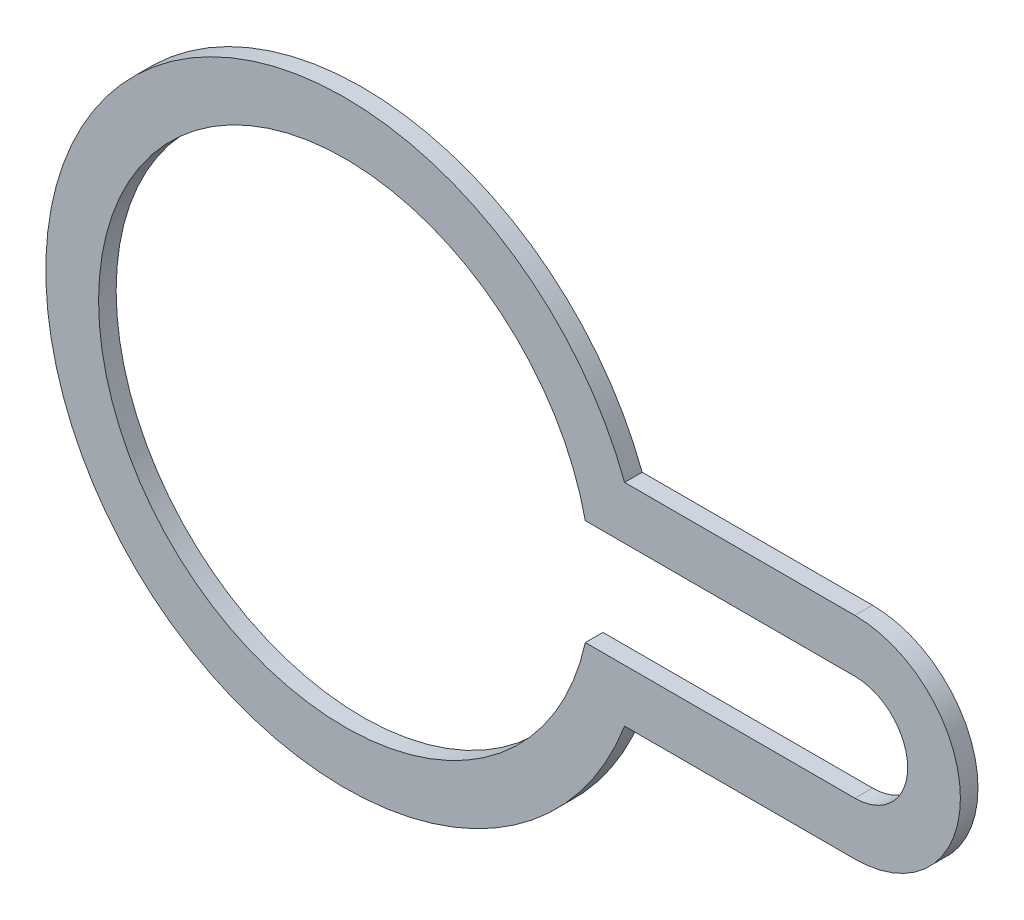
SolidWorks part; units mm, degrees
material "1060-O (SS)"
ref_plane "Ebene vorne" through (0, 0, 0) normal (0, 0, 1) x (1, 0, 0)
ref_plane "Ebene oben" through (0, 0, 0) normal (0, 1, 0) x (1, 0, 0)
ref_plane "Ebene rechts" through (0, 0, 0) normal (1, 0, 0) x (0, 0, -1)
sketch "Sketch1" plane through (0, 0, 0) normal (0, 0, 1) x (1, 0, 0)
  line L0 (29, 6) -> (15.906, 6)
  line L1 (13.6748, 3) -> (29, 3)
  line L2 (0, 0) -> (34.437, 0) construction
  line L3 (13.6748, -3) -> (29, -3)
  line L4 (29, -6) -> (15.906, -6)
  arc A0 (15.906, -6) -> (15.906, 6) centre (0, 0) cw
  arc A1 (29, 6) -> (29, -6) centre (29, 0) cw
  arc A2 (13.6748, -3) -> (13.6748, 3) centre (0, 0) cw
  arc A3 (29, 3) -> (29, -3) centre (29, 0) cw
  point P11 (30.2379, 0)
  point P13 (28.0444, 0)
  point P14 (0, 0)
  point P15 (33.6222, 0)
  point P16 (0, 0)
  point P17 (0, 0)
  dimension "D1" = 14
  dimension "D2" = 3
  dimension "D4" = 3
  dimension "D3" = 3
  dimension "D5" = 29
extrude "Boss-Extrude1" add sketch "Sketch1" along normal blind 1 contours A0 L0 A1 L4 | A2 L1 A3 L3
equation "\"1§\"=10"
